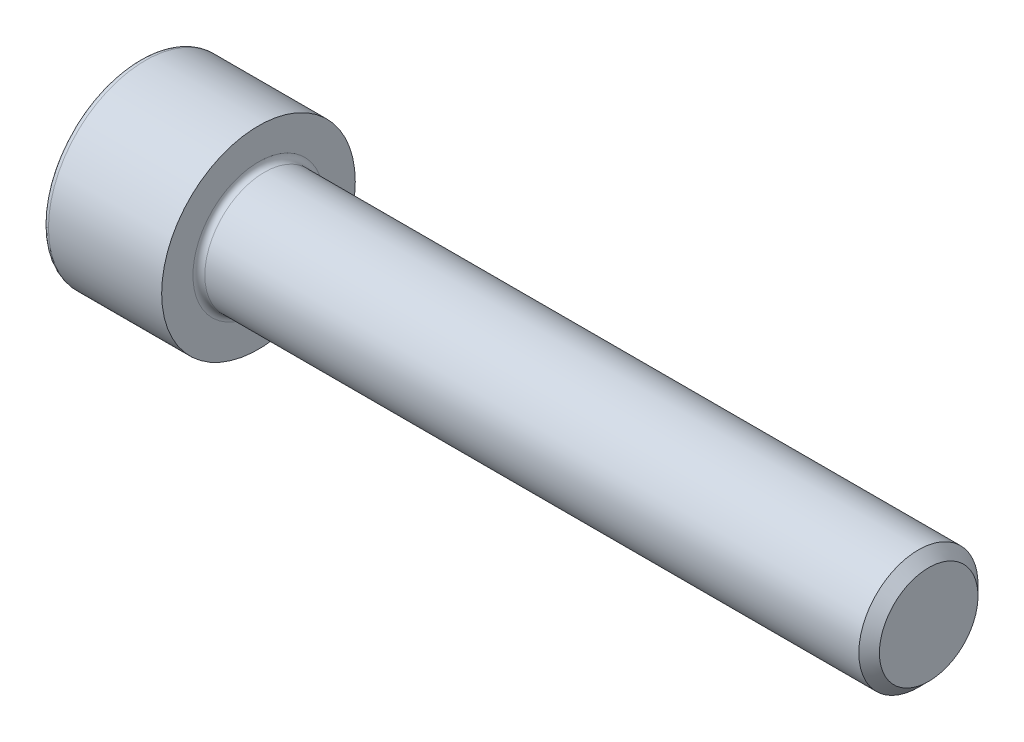
SolidWorks part; units mm, degrees
revolve "Base-Revolve" add sketch "BodySke"
sketch "BodySke" plane through (0, 0, 0) normal (0, 0, 1) x (1, 0, 0)
  line L0 (0, 0) -> (0, 6.5)
  line L1 (0, 6.5) -> (8, 6.5)
  line L2 (8, 6.5) -> (8, 4)
  line L3 (8, 4) -> (52.3095, 4)
  line L4 (53, 3.3095) -> (53, 0)
  line L5 (53, 0) -> (0, 0)
  line L6 (-31.75, 0) -> (127, 0) construction
  line L8 (53, 3.3095) -> (52.3095, 4)
  line L10 (53, -3.3095) -> (52.3095, -4) construction
  line L11 (9.25, 9.525) -> (9.25, 3.175) construction
  line L12 (25, 9.525) -> (25, 3.175) construction
  line L13 (-7, 9.525) -> (-7, 3.175) construction
  dimension "Body_ch_ang" = 45
  dimension "Thread_length" = 60
cosmetic thread "ThreadCosmetic" [suppressed]
fillet "Fillet1" radius 0.4 1 edges at (8, 0, 4)
fillet "Fillet2" radius 0.4 1 edges at (0, 0, 6.5)
ref_plane "Plane1" through (0, 0, 0) normal (0, 0, 1) x (1, 0, 0)
ref_plane "Plane2" through (0, 0, 0) normal (0, 1, 0) x (1, 0, 0)
ref_plane "Plane3" through (0, 0, 0) normal (1, 0, 0) x (0, 0, -1)
sketch "Sketch2" plane through (0, 0, 0) normal (0, 0, 1) x (1, 0, 0)
  line L0 (0, 3.0475) -> (4, 3.0475)
  line L1 (4, 3.0475) -> (5.7595, 0)
  line L2 (-31.75, 0) -> (127, 0) construction
  line L3 (5.7595, 0) -> (0, 0)
  line L4 (0, 0) -> (0, 3.0475)
  line L6 (0, 0) -> (47.625, 0) construction
  dimension "D2" = 60
revolve "Hex-PreBroach" cut sketch "Sketch2" angle 360 about L6
sketch "Sketch3" plane through (0, 0, 0) normal (-1, 0, 0) x (0, 0.5, 0.866)
  line L0 (1.7595, 3.0475) -> (-1.7595, 3.0475)
  line L1 (-1.7595, 3.0475) -> (-3.5189, 0)
  line L2 (1.7595, 3.0475) -> (3.5189, 0)
  line L3 (1.7595, -3.0475) -> (3.5189, 0)
  line L4 (1.7595, -3.0475) -> (-1.7595, -3.0475)
  line L5 (-1.7595, -3.0475) -> (-3.5189, 0)
extrude "Hex" cut sketch "Sketch3" against normal blind 4
sketch "ThdSchSke" plane through (0, 0, 0) normal (0, 0, 1) x (1, 0, 0)
  line L0 (25, -3.3095) -> (24.5165, -4)
  line L1 (25, -3.3095) -> (25.4835, -4)
  line L2 (25.4835, -4) -> (25.4835, -5)
  line L3 (-3.175, 0) -> (5.1513, 0) construction
  line L4 (0, 6.1) -> (0, -6.1) construction
  line L5 (25.4835, -5) -> (24.5165, -5)
  line L6 (24.5165, -5) -> (24.5165, -4)
revolve "ThreadSchematic" [suppressed] cut sketch "ThdSchSke" angle 360 about L3
pattern_linear "ThdSchPat" [suppressed]
equation "\"D2@Sketch3\" = \"Hex_size@Sketch3\" / 2"
equation "\"D1@Sketch3\" = \"Hex_size@Sketch3\" / 2"
equation "\"D1@Sketch2\" = \"Hex_size@Sketch3\" / 2"
equation "\"Thread_minor@ThreadCosmetic\"  =  \"Minor_dia@BodySke\""
equation "\"Depth@Sketch2\" =  \"Key_eng@Hex\""
equation "\"Thread_length@ThreadCosmetic\" = ((sgn( (\"Length@BodySke\" - \"Advance@BodySke\" * 3.0) - \"Thread_nom@BodySke\" )-1)*( (\"Length@BodySke\" - \"Advance@BodySke\" * 3.0) - \"Thread_nom@BodySke\" ))/-2+ \"Thread_nom@BodySke\""
equation "\"Thread_minor@ThdSchSke\" = \"Minor_dia@BodySke\""
equation "\"Diameter@ThdSchSke\" = \"Diameter@BodySke\""
equation "\"Overcut@ThdSchSke\" = \"Diameter@BodySke\" * 1.25"
equation "\"Start@ThdSchSke\" = \"Head_ht@BodySke\" + \"Length@BodySke\" - \"Thread_length@ThreadCosmetic\"  '---Non-countersunk---"
equation "\"Num_threads@ThdSchPat\" = int( \"Thread_length@ThreadCosmetic\" / \"Advance@BodySke\" + 0.999 )  + 1"
equation "\"Advance@ThdSchPat\" = \"Thread_length@ThreadCosmetic\" /  (\"Num_threads@ThdSchPat\" - 1) 'relax it"
equation "\"Num_threads@ThdSchPat\" = \"Num_threads@ThdSchPat\" - sgn( \"Num_threads@ThdSchPat\" - 1) '---chamfered tips only---"
